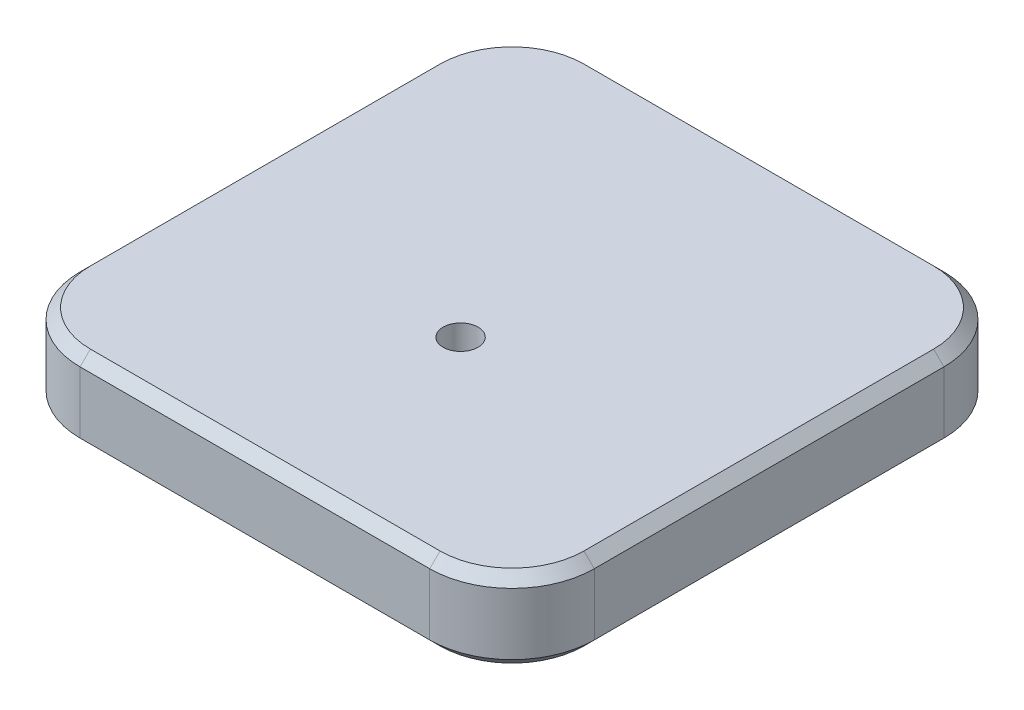
SolidWorks part; units mm, degrees
material "PBT (一般用)"
ref_plane "Front Plane" through (0, 0, 0) normal (0, 0, 1) x (1, 0, 0)
ref_plane "Top Plane" through (0, 0, 0) normal (0, 1, 0) x (1, 0, 0)
ref_plane "Right Plane" through (0, 0, 0) normal (1, 0, 0) x (0, 0, -1)
sketch "Sketch1" plane through (0, 0, 0) normal (0, 1, 0) x (1, 0, 0)
  line L1 (-17.6883, 15.9444) -> (7.3117, 15.9444)
  line L2 (-17.6883, 15.9444) -> (-17.6883, -9.0556)
  line L3 (-17.6883, -9.0556) -> (7.3117, -9.0556)
  line L4 (7.3117, 15.9444) -> (7.3117, -9.0556)
  dimension "D1" = 25
  dimension "D2" = 25
extrude "Boss-Extrude1" add sketch "Sketch1" along normal blind 4
fillet "Fillet1" radius 4 4 edges at (-17.6883, 2, -15.9444) (7.3117, 2, -15.9444) (7.3117, 2, 9.0556) (-17.6883, 2, 9.0556)
sketch "Sketch2" plane through (0, 4, 0) normal (0, 1, 0) x (1, 0, 0)
  line L0 (-5.1883, 15.9444) -> (-5.1883, -9.0556) construction
  line L3 (3.3117, 15.9444) -> (-13.6883, 15.9444) construction
  line L4 (-13.6883, -9.0556) -> (3.3117, -9.0556) construction
  line L5 (-17.6883, 3.4444) -> (7.3117, 3.4444) construction
  line L6 (-17.6883, 11.9444) -> (-17.6883, -5.0556) construction
  line L7 (7.3117, -5.0556) -> (7.3117, 11.9444) construction
  circle A0 centre (-5.1883, 0.9444) radius 1.7
  point P12 (-5.1883, 3.4444)
  point P13 (-5.1883, 0.9444)
  dimension "D1" = 2.5
hole_wizard "Ø1.7 (1.7) Diameter Hole1" positions "3DSketch1" profile "Sketch3" hole size "Ø1.7" standard "ANSI Metric"
sketch3d "3DSketch1"
  point P0 (-5.1883, 4, -0.9444)
sketch "Sketch3" plane through (-5.1883, 4, -0.9444) normal (1, 0, 0) x (0, 0, 1)
  line L0 (0, 0) -> (0, 8.5)
  line L1 (0, 8.5) -> (0.85, 8.5)
  line L2 (0.85, 8.5) -> (0.85, 0)
  line L5 (0.85, 0) -> (0, 0)
  line L10 (0, 8.5) -> (-0.85, 8.5) construction
  line L11 (0, -6.35) -> (0, 107.95) construction
  dimension "Hole Dia." = 1.7
  dimension "Hole Depth" = 8.5
  dimension "Drill Angle" = 180
chamfer "Chamfer1" distance 0.5 angle 45 16 edges at (6.1401, 0, -14.7728) (-5.1883, 0, -15.9444) (-16.5167, 0, -14.7728) (-17.6883, 0, -3.4444) (-16.5167, 0, 7.8841) (-5.1883, 0, 9.0556) (6.1401, 0, 7.8841) (7.3117, 0, -3.4444) (6.1401, 4, 7.8841) (-5.1883, 4, 9.0556) (-16.5167, 4, 7.8841) (-17.6883, 4, -3.4444) (-16.5167, 4, -14.7728) (-5.1883, 4, -15.9444) (6.1401, 4, -14.7728) (7.3117, 4, -3.4444)
